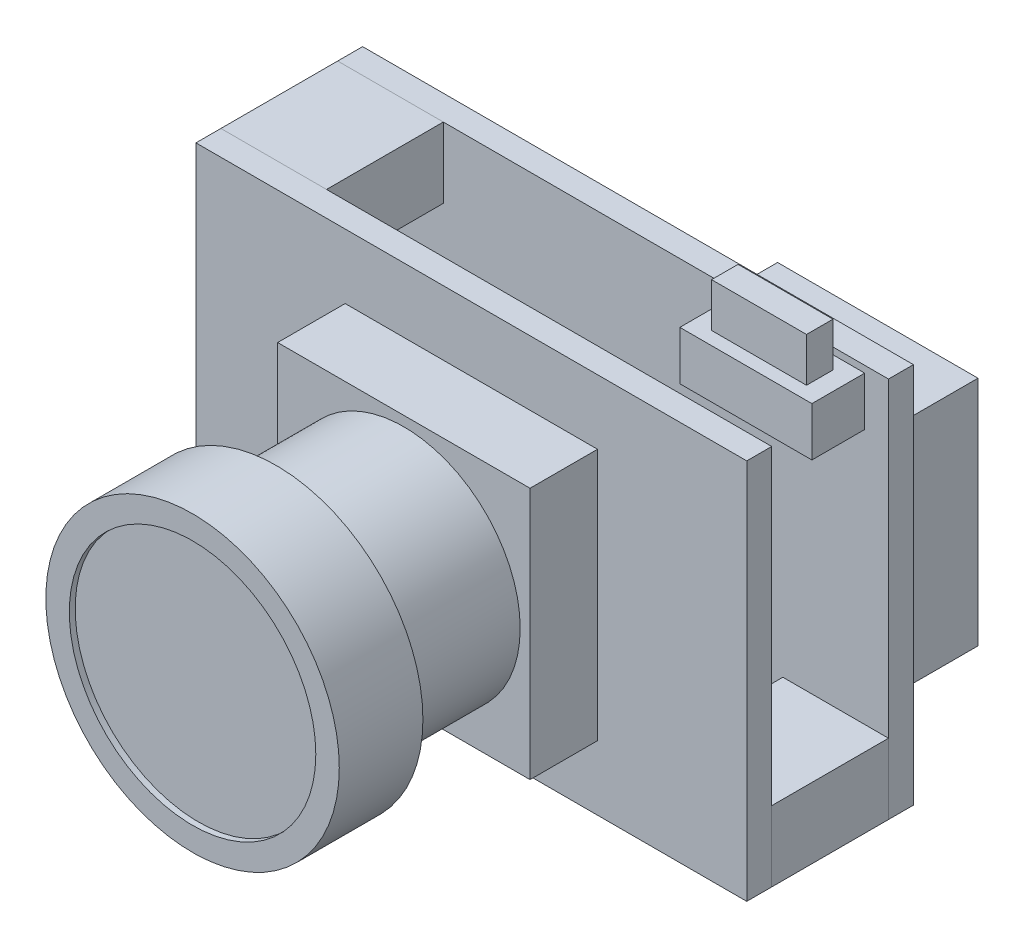
SolidWorks part; units mm, degrees
ref_plane "Front Plane" through (0, 0, 0) normal (0, 0, 1) x (1, 0, 0)
ref_plane "Top Plane" through (0, 0, 0) normal (0, 1, 0) x (1, 0, 0)
ref_plane "Right Plane" through (0, 0, 0) normal (1, 0, 0) x (0, 0, -1)
sketch "Sketch1" plane through (0, 0, 0) normal (0, 0, 1) x (1, 0, 0)
  line L1 (-9.385, 6.5) -> (9.385, 6.5)
  line L2 (-9.385, 6.5) -> (-9.385, -6.5)
  line L3 (-9.385, -6.5) -> (9.385, -6.5)
  line L4 (9.385, 6.5) -> (9.385, -6.5)
  line L5 (-9.385, 6.5) -> (9.385, -6.5) construction
  line L6 (-9.385, -6.5) -> (9.385, 6.5) construction
  point P0 (0, 0)
  dimension "D1" = 13
  dimension "D2" = 18.77
extrude "Boss-Extrude1" add sketch "Sketch1" along normal blind 0.85
sketch "Sketch2" plane through (0, 0, 0.85) normal (0, 0, 1) x (1, 0, 0)
  line L1 (9.385, -6.5) -> (5.785, -6.5)
  line L2 (9.385, -6.5) -> (9.385, -4.1)
  line L3 (9.385, -4.1) -> (5.785, -4.1)
  line L4 (5.785, -6.5) -> (5.785, -4.1)
  line L5 (-9.385, 6.5) -> (-5.785, 6.5)
  line L6 (-9.385, 6.5) -> (-9.385, 4.1)
  line L7 (-9.385, 4.1) -> (-5.785, 4.1)
  line L8 (-5.785, 6.5) -> (-5.785, 4.1)
  dimension "D1" = 2.4
  dimension "D2" = 3.6
extrude "Boss-Extrude2" add sketch "Sketch2" along normal blind 3.98 separate body
sketch "Sketch3" plane through (0, 0, 4.83) normal (0, 0, 1) x (1, 0, 0)
  line L0 (9.385, -6.5) -> (9.385, -4.1) construction
  line L1 (-9.385, 6.5) -> (9.385, 6.5)
  line L2 (-9.385, 6.5) -> (-9.385, -6.5)
  line L3 (-9.385, -6.5) -> (9.385, -6.5)
  line L4 (9.385, 6.5) -> (9.385, -6.5)
  line L5 (5.785, -6.5) -> (9.385, -6.5) construction
extrude "Boss-Extrude3" add sketch "Sketch3" along normal blind 0.85
sketch "Sketch4" plane through (0, 0, 5.68) normal (0, 0, 1) x (1, 0, 0)
  line L1 (-4.3, 4.3) -> (4.3, 4.3)
  line L2 (-4.3, 4.3) -> (-4.3, -4.3)
  line L3 (-4.3, -4.3) -> (4.3, -4.3)
  line L4 (4.3, 4.3) -> (4.3, -4.3)
  line L5 (-4.3, 4.3) -> (4.3, -4.3) construction
  line L6 (-4.3, -4.3) -> (4.3, 4.3) construction
  point P0 (0, 0)
  dimension "D1" = 8.6
extrude "Boss-Extrude4" add sketch "Sketch4" along normal blind 2.3
sketch "Sketch5" plane through (0, 0, 7.98) normal (0, 0, 1) x (1, 0, 0)
  circle A0 centre (0, 0) radius 3.965
  dimension "D1" = 7.93
extrude "Boss-Extrude5" add sketch "Sketch5" along normal blind 4.35
sketch "Sketch6" plane through (0, 0, 12.33) normal (0, 0, 1) x (1, 0, 0)
  circle A0 centre (0, 0) radius 5
  dimension "D1" = 10
extrude "Boss-Extrude6" add sketch "Sketch6" along normal blind 2.85
sketch "Sketch7" plane through (0, 0, 15.18) normal (0, 0, 1) x (1, 0, 0)
  circle A0 centre (0, 0) radius 4.2
  circle A1 centre (0, 0) radius 5 construction
  dimension "D1" = 0.8
extrude "Cut-Extrude1" cut sketch "Sketch7" against normal blind 0.2
sketch "Sketch8" plane through (0, 0, 0) normal (0, 0, -1) x (-1, 0, 0)
  line L0 (-9.385, -6.5) -> (-9.385, 6.5) construction
  line L1 (-9.285, 4.9) -> (-2.455, 4.9)
  line L2 (-9.285, 4.9) -> (-9.285, -3)
  line L3 (-9.285, -3) -> (-2.455, -3)
  line L4 (-2.455, 4.9) -> (-2.455, -3)
  line L5 (-9.385, 6.5) -> (9.385, 6.5) construction
  dimension "D1" = 7.9
  dimension "D2" = 6.83
  dimension "D3" = 0.1
  dimension "D4" = 1.6
extrude "Boss-Extrude7" add sketch "Sketch8" along normal blind 2.3
sketch "Sketch9" plane through (0, 0, 0) normal (0, 0, -1) x (-1, 0, 0)
  line L1 (-0.6481, -5.1764) -> (5.3519, -5.1764)
  line L2 (-0.6481, -5.1764) -> (-0.6481, 0.8236)
  line L3 (-0.6481, 0.8236) -> (5.3519, 0.8236)
  line L4 (5.3519, -5.1764) -> (5.3519, 0.8236)
  dimension "D1" = 6
extrude "Boss-Extrude8" add sketch "Sketch9" along normal blind 1
sketch "Sketch10" plane through (0, 0, 0.85) normal (0, 0, 1) x (1, 0, 0)
  line L1 (8.5749, 6.2701) -> (4.0749, 6.2701)
  line L2 (8.5749, 6.2701) -> (8.5749, 4.6059)
  line L3 (8.5749, 4.6059) -> (4.0749, 4.6059)
  line L4 (4.0749, 6.2701) -> (4.0749, 4.6059)
  dimension "D1" = 4.5
extrude "Boss-Extrude9" add sketch "Sketch10" along normal blind 1.8
sketch "Sketch11" plane through (0, 6.2701, 0) normal (0, 1, 0) x (1, 0, 0)
  line L0 (8.5749, -0.85) -> (4.0749, -2.65) construction
  line L1 (8.5749, -2.65) -> (4.0749, -2.65) construction
  line L2 (4.0749, -2.65) -> (4.0749, -0.85) construction
  line L4 (4.7074, -1.2989) -> (7.9423, -1.2989)
  line L5 (4.7074, -1.2989) -> (4.7074, -2.2011)
  line L6 (4.7074, -2.2011) -> (7.9423, -2.2011)
  line L7 (7.9423, -1.2989) -> (7.9423, -2.2011)
  line L8 (4.7074, -1.2989) -> (7.9423, -2.2011) construction
  line L9 (4.7074, -2.2011) -> (7.9423, -1.2989) construction
  point P7 (6.3249, -1.75)
extrude "Boss-Extrude10" add sketch "Sketch11" along normal blind 1.5
sketch "Sketch12" plane through (0, 0, 0.85) normal (0, 0, 1) x (1, 0, 0)
  line L1 (-3.6639, 1.1451) -> (-6.0818, 1.1451)
  line L2 (-3.6639, 1.1451) -> (-3.6639, -1.1451)
  line L3 (-3.6639, -1.1451) -> (-6.0818, -1.1451)
  line L4 (-6.0818, 1.1451) -> (-6.0818, -1.1451)
  line L5 (-3.6639, 1.1451) -> (-6.0818, -1.1451) construction
  line L6 (-3.6639, -1.1451) -> (-6.0818, 1.1451) construction
  point P0 (-4.8729, 0)
extrude "Boss-Extrude11" add sketch "Sketch12" along normal blind 1.5
sketch "Sketch13" plane through (-6.0818, 0, 0) normal (-1, 0, 0) x (0, 0, 1)
  line L0 (1.6, 1.1451) -> (1.6, -1.1451) construction
  line L1 (2.35, 1.1451) -> (0.85, 1.1451) construction
  line L2 (2.35, -1.1451) -> (0.85, -1.1451) construction
  line L3 (2.35, 0) -> (0.85, 0) construction
  line L4 (2.35, 1.1451) -> (2.35, -1.1451) construction
  line L5 (0.85, 1.1451) -> (0.85, -1.1451) construction
  circle A0 centre (1.6, 0.55) radius 0.45
  circle A1 centre (1.6, -0.55) radius 0.45
  dimension "D1" = 0.9
  dimension "D2" = 1.1
extrude "Boss-Extrude13" add sketch "Sketch13" along normal blind 4
